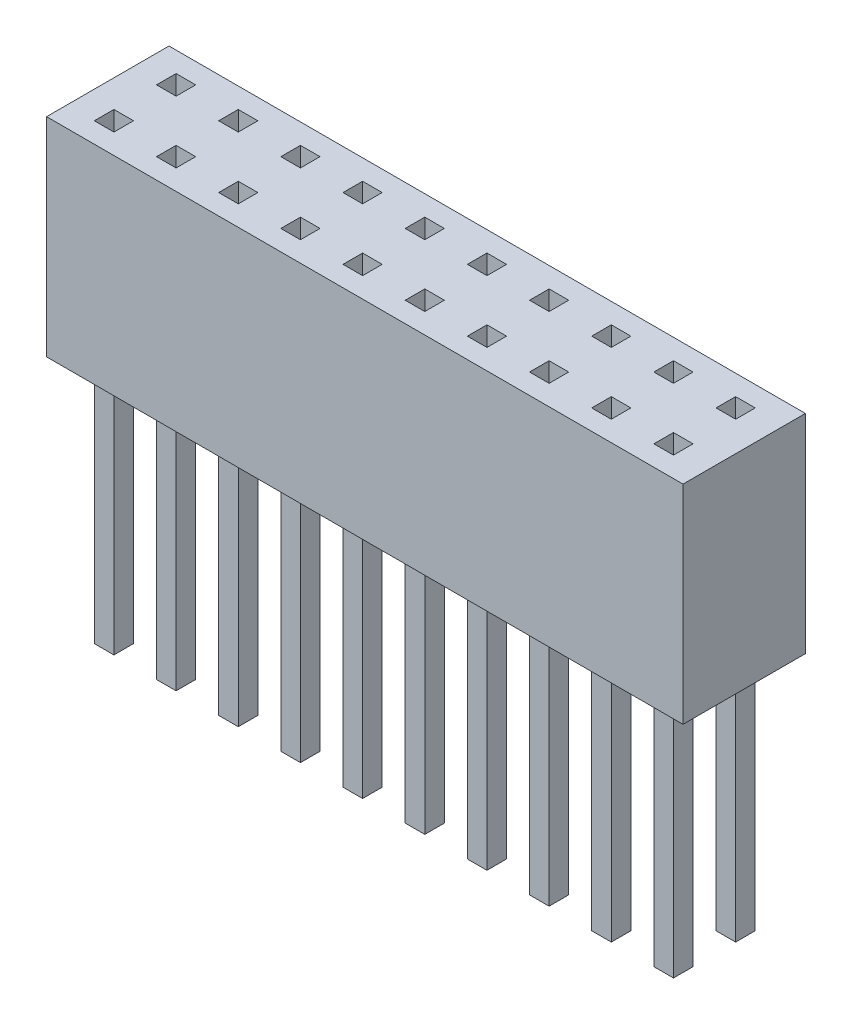
SolidWorks part; units mm, degrees
ref_plane "Ebene vorne" through (0, 0, 0) normal (0, 0, 1) x (1, 0, 0)
ref_plane "Ebene oben" through (0, 0, 0) normal (0, 1, 0) x (1, 0, 0)
ref_plane "Ebene rechts" through (0, 0, 0) normal (1, 0, 0) x (0, 0, -1)
sketch "Skizze1" plane through (0, 0, 0) normal (0, 1, 0) x (1, 0, 0)
  line L0 (0, 6.8939) -> (0, -5.8333) construction
  line L1 (-16.8636, 0) -> (16.5909, 0) construction
  line L2 (-13, -2.5) -> (-13, 2.5)
  line L3 (-13, 2.5) -> (13, 2.5)
  line L4 (13, -2.5) -> (13, 2.5)
  line L5 (-13, -2.5) -> (13, -2.5)
  point P9 (0, 2.5)
  point P10 (0, -2.5)
  point P12 (13, 0)
  point P13 (-13, 0)
  dimension "D1" = 5
  dimension "D2" = 26
extrude "Aufsatz-Linear austragen1" add sketch "Skizze1" along normal blind 8.5
sketch "Skizze2" plane through (0, 0, 0) normal (0, 1, 0) x (1, 0, 0)
  line L0 (-13, -2.5) -> (13, -2.5) construction
  line L1 (-11.88, -1.67) -> (-11.08, -1.67)
  line L2 (-11.88, -1.67) -> (-11.88, -0.87)
  line L3 (-11.88, -0.87) -> (-11.08, -0.87)
  line L4 (-11.08, -1.67) -> (-11.08, -0.87)
  line L5 (-11.88, -1.67) -> (-11.08, -0.87) construction
  line L6 (-11.88, -0.87) -> (-11.08, -1.67) construction
  line L7 (-13, 2.5) -> (-13, -2.5) construction
  point P0 (-11.48, -1.27)
  dimension "D1" = 0.8
  dimension "D2" = 0.83
  dimension "D3" = 1.12
extrude "Aufsatz-Linear austragen2" add sketch "Skizze2" against normal blind 10
sketch "Skizze3" plane through (0, 8.5, 0) normal (0, 1, 0) x (1, 0, 0)
  line L8 (-11.88, -1.67) -> (-11.08, -1.67)
  line L9 (-11.08, -1.67) -> (-11.08, -0.87)
  line L10 (-11.08, -0.87) -> (-11.88, -0.87)
  line L11 (-11.88, -0.87) -> (-11.88, -1.67)
  line L12 (-11.88, -1.67) -> (-11.08, -1.67)
  line L13 (-11.08, -1.67) -> (-11.08, -0.87)
  line L14 (-11.08, -0.87) -> (-11.88, -0.87)
  line L15 (-11.88, -0.87) -> (-11.88, -1.67)
  dimension "D1" = 0
extrude "Schnitt-Linear austragen1" cut sketch "Skizze3" against normal blind 7
pattern_linear "Lineares Muster1" count 10 spacing 2.54 along (1, 0, 0) count 2 spacing 2.54 along (0, 0, -1) of "Aufsatz-Linear austragen2", "Schnitt-Linear austragen1"
